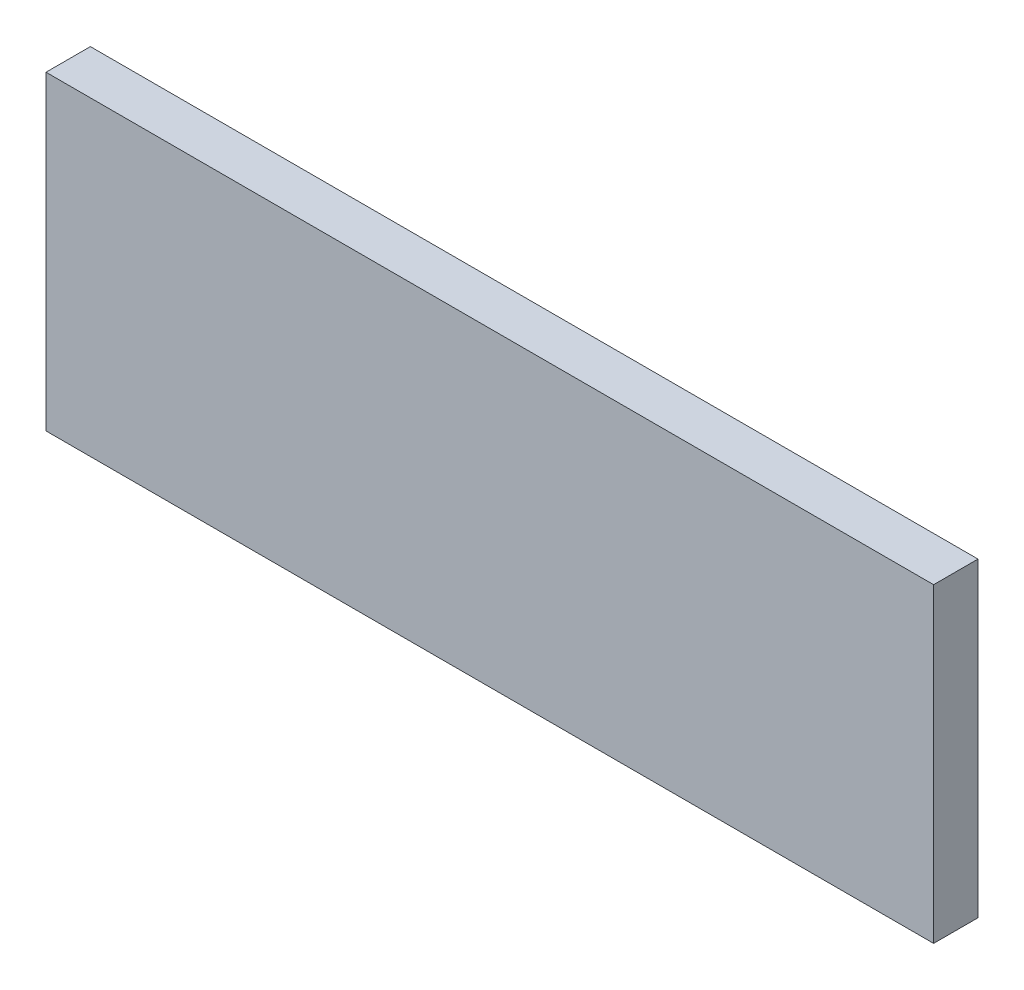
SolidWorks part; units mm, degrees
material "Cedar"
ref_plane "Front Plane" through (0, 0, 0) normal (0, 0, 1) x (1, 0, 0)
ref_plane "Top Plane" through (0, 0, 0) normal (0, 1, 0) x (1, 0, 0)
ref_plane "Right Plane" through (0, 0, 0) normal (1, 0, 0) x (0, 0, -1)
sketch "Sketch1" plane through (0, 0, 0) normal (0, 0, 1) x (1, 0, 0)
  line L1 (-125.2953, 74.2226) -> (128.7047, 74.2226)
  line L2 (-125.2953, 74.2226) -> (-125.2953, -14.6774)
  line L3 (-125.2953, -14.6774) -> (128.7047, -14.6774)
  line L4 (128.7047, 74.2226) -> (128.7047, -14.6774)
  dimension "D1" = 254
  dimension "D2" = 88.9
extrude "Boss-Extrude1" add sketch "Sketch1" along normal blind 12.7
